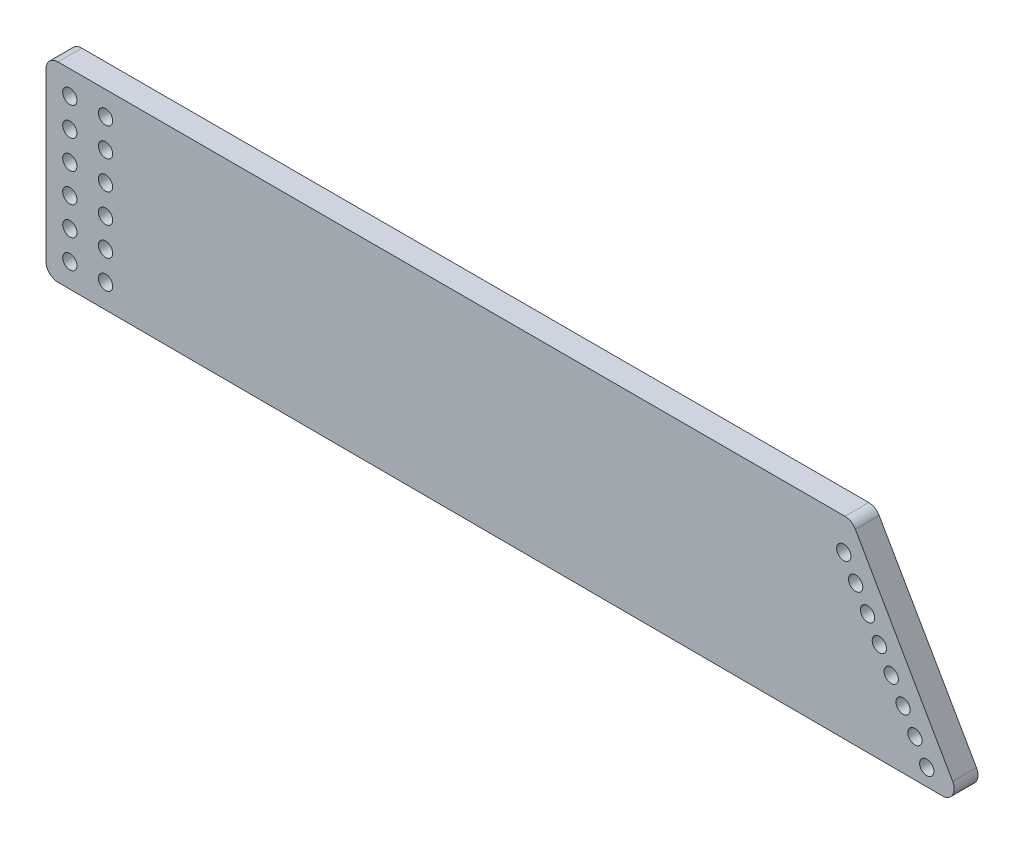
SolidWorks part; units mm, degrees
ref_plane "Front Plane" through (0, 0, 0) normal (0, 0, 1) x (1, 0, 0)
ref_plane "Top Plane" through (0, 0, 0) normal (0, 1, 0) x (1, 0, 0)
ref_plane "Right Plane" through (0, 0, 0) normal (1, 0, 0) x (0, 0, -1)
sketch "Sketch1" plane through (0, 0, 0) normal (0, 0, 1) x (1, 0, 0)
  line L0 (-169.15, 40.0548) -> (169.15, 40.0548)
  line L1 (169.15, 40.0548) -> (215.7411, -41.2017)
  line L2 (215.7411, -41.2017) -> (-169.15, -40.0548)
  line L3 (-169.15, -40.0548) -> (-169.15, 40.0548)
  point P4 (0, 40.0548)
  point P6 (178.9834, 48.0667)
  point P7 (-169.15, 0)
  dimension "D1" = 338.3
  dimension "D2" = 93.6661
  dimension "D3" = 60
  dimension "D4" = 80.1095
extrude "Boss-Extrude1" add sketch "Sketch1" along normal blind 10
fillet "Fillet1" radius 5 4 edges at (215.7411, -41.2017, 5) (169.15, 40.0548, 5) (-169.15, -40.0548, 5) (-169.15, 40.0548, 5)
sketch "Sketch2" plane through (0, 0, 0) normal (0, 0, -1) x (-1, 0, 0)
  line L0 (0, 0) -> (169.15, -0.0074) construction
  line L1 (169.15, 35.0548) -> (169.15, -35.0696) construction
  line L2 (-166.2533, 40.0548) -> (164.15, 40.0548) construction
  line L3 (-161.7837, 33.6114) -> (-201.5771, -35.7896) construction
  line L4 (-211.4334, -33.6888) -> (-170.5909, 37.5418) construction
  line L5 (-161.7837, 33.6114) -> (144.15, 33.6114) construction
  line L6 (0, 0) -> (0, 33.6114) construction
  line L7 (-200.5823, -34.0545) -> (0, -34.0545) construction
  line L8 (0, -34.0545) -> (0, 0) construction
  circle A0 centre (144.15, 30.0548) radius 3
  circle A2 centre (159.15, 30.0548) radius 3
  circle A3 centre (159.15, 18.0548) radius 3
  circle A4 centre (159.15, 6.0548) radius 3
  circle A5 centre (144.15, 18.0548) radius 3
  circle A6 centre (144.15, 6.0548) radius 3
  circle A7 centre (144.1495, -6.0674) radius 3
  circle A8 centre (144.1484, -18.0674) radius 3
  circle A9 centre (159.1495, -6.0688) radius 3
  circle A10 centre (159.1484, -18.0688) radius 3
  circle A11 centre (159.1474, -30.0688) radius 3
  circle A12 centre (144.1474, -30.0674) radius 3
  circle A13 centre (-165.7631, 26.6713) radius 3
  circle A14 centre (-195.6081, -25.3794) radius 3
  circle A15 centre (-190.6339, -16.7043) radius 3
  circle A16 centre (-185.6598, -8.0292) radius 3
  circle A17 centre (-180.6856, 0.6459) radius 3
  circle A18 centre (-175.7114, 9.321) radius 3
  circle A19 centre (-170.7372, 17.9962) radius 3
  circle A20 centre (-200.5823, -34.0545) radius 3
  point P52 (0, 0)
  point P54 (0, 0)
  point P56 (0, -33.0221)
  point P58 (-200.5823, -34.0545)
  dimension "D1" = 6
  dimension "D2" = 10
  dimension "D6" = 25
  dimension "D7" = 12
  dimension "D8" = 6
  dimension "D9" = 10
  dimension "D10" = 10
  dimension "D11" = 10
  dimension "D12" = 10
  dimension "D13" = 10
  dimension "D14" = 10
  dimension "D15" = 8
  dimension "D17" = 6
  dimension "D18" = 10
  dimension "D5" = 15
  dimension "D16" = 80
  dimension "D3" = 2
  dimension "D4" = 3
extrude "Cut-Extrude1" cut sketch "Sketch2" against normal blind 15
